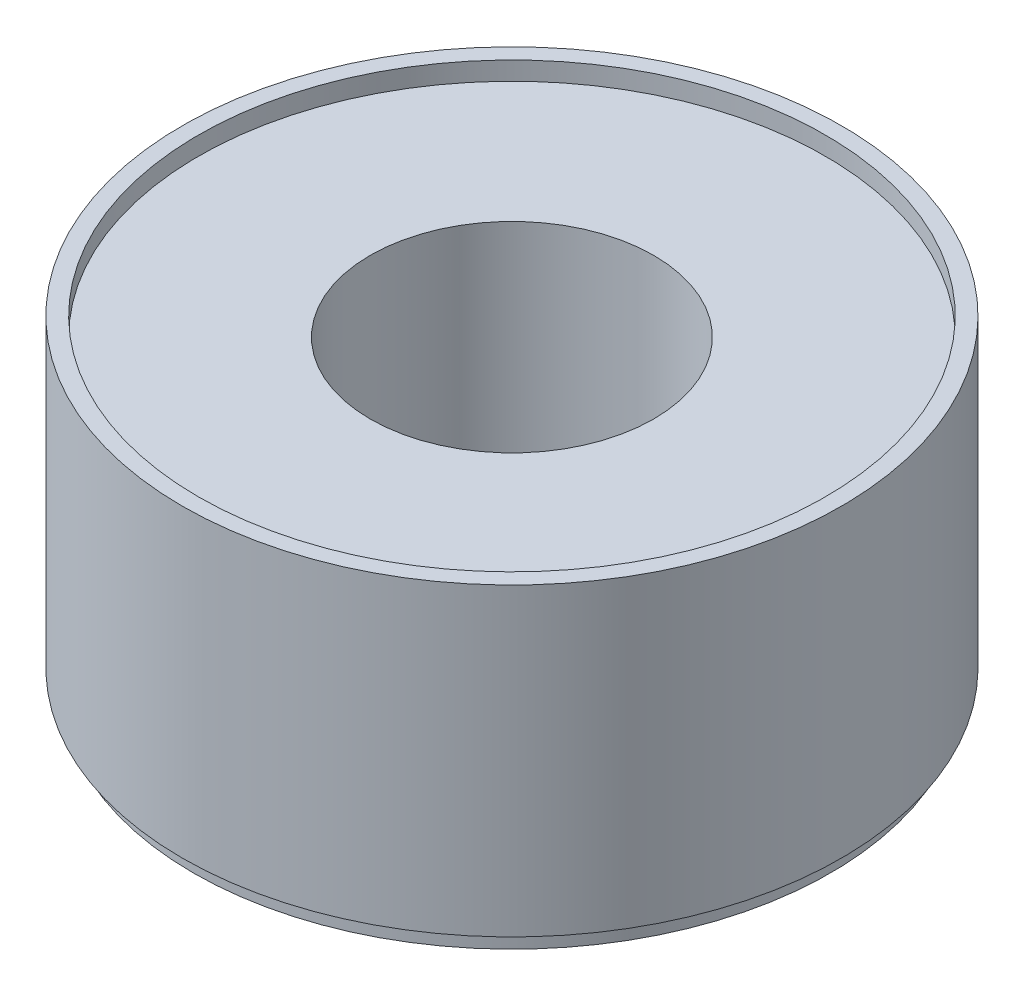
SolidWorks part; units mm, degrees
ref_plane "Alzado" through (0, 0, 0) normal (0, 0, 1) x (1, 0, 0)
ref_plane "Planta" through (0, 0, 0) normal (0, 1, 0) x (1, 0, 0)
ref_plane "Vista lateral" through (0, 0, 0) normal (1, 0, 0) x (0, 0, -1)
sketch "Croquis1" plane through (0, 0, 0) normal (1, 0, 0) x (0, 0, -1)
  line L0 (0, 73.2368) -> (0, -85.7231) construction
  line L1 (73.9572, -85.7231) -> (166.1635, -85.7231)
  line L2 (166.1635, -85.7231) -> (166.1635, -76.1183)
  line L3 (166.1635, -76.1183) -> (162.8019, -76.1183)
  line L4 (162.8019, -76.1183) -> (171.9264, -76.1183)
  line L5 (171.9264, -76.1183) -> (171.9264, 82.8881)
  line L6 (171.9264, 82.8881) -> (163.5222, 82.8881)
  line L7 (163.5222, 82.8881) -> (163.5222, 73.2832)
  line L8 (148.8749, 73.2832) -> (97.9693, 73.2832)
  line L9 (97.9693, 73.2832) -> (73.9572, 73.2832)
  line L10 (73.9572, 73.2832) -> (73.9572, -85.7231)
  line L11 (148.8749, 73.2832) -> (163.5222, 73.2832)
revolve "Revolución2" add sketch "Croquis1" angle 360 about L0
